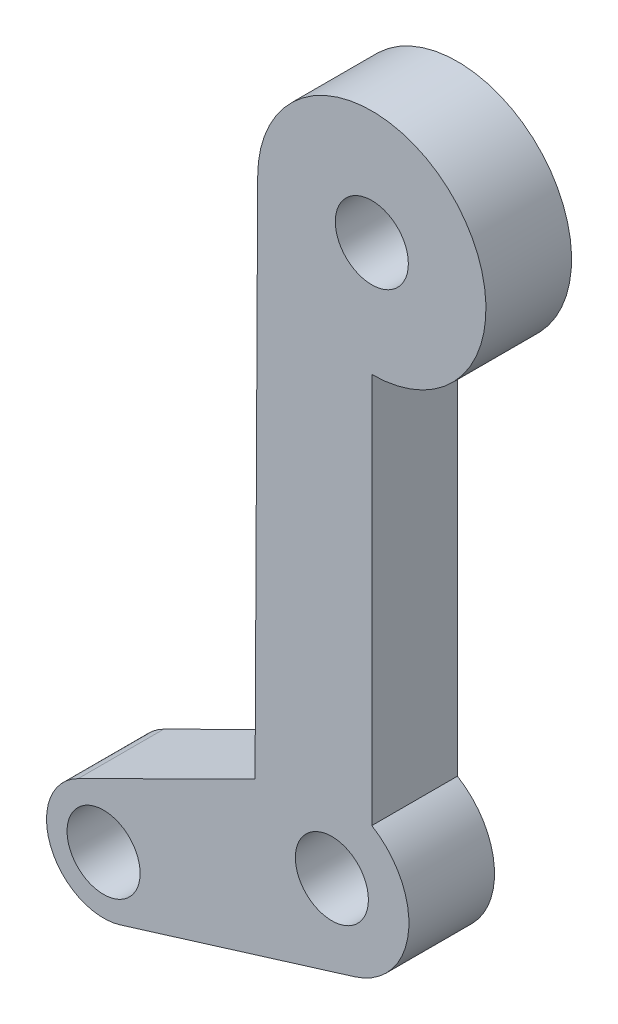
SolidWorks part; units mm, degrees
ref_plane "Front Plane" through (0, 0, 0) normal (0, 0, 1) x (1, 0, 0)
ref_plane "Top Plane" through (0, 0, 0) normal (0, 1, 0) x (1, 0, 0)
ref_plane "Right Plane" through (0, 0, 0) normal (1, 0, 0) x (0, 0, -1)
sketch "Sketch1" plane through (0, 0, 0) normal (0, 0, 1) x (1, 0, 0)
  line L0 (-5, 0) -> (-5.125, -24.9831)
  line L1 (-12.864, -26.7619) -> (-3.2539, -21.9786)
  line L2 (-11.0132, -31.3889) -> (-0.7553, -28.2251)
  line L3 (0, -5) -> (0, -22.1142)
  circle A0 centre (0, 0) radius 1.6
  circle A1 centre (0, 0) radius 5
  circle A2 centre (-1.75, -25) radius 1.6
  circle A3 centre (-11.75, -29) radius 1.6
  circle A4 centre (-1.75, -25) radius 3.375
  circle A5 centre (-11.75, -29) radius 2.5
  dimension "D1" = 3.2
  dimension "D2" = 10
  dimension "D3" = 25
  dimension "D6" = 1.75
  dimension "D7" = 6.75
  dimension "D8" = 5
  dimension "D4" = 10
  dimension "D5" = 4
extrude "Boss-Extrude1" add sketch "Sketch1" along normal blind 3.75
